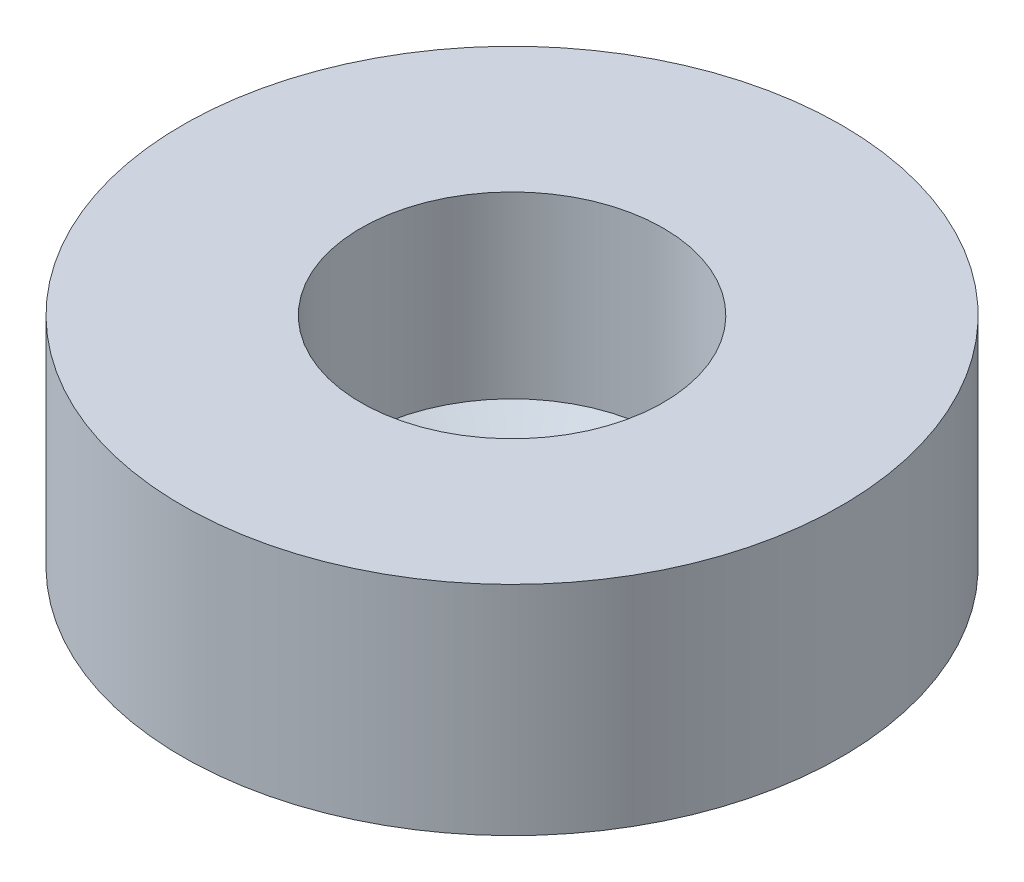
SolidWorks part; units mm, degrees
material "Delrin 2700 NC010, Low Viscosity Acetal Copolymer (SS)"
ref_plane "Front Plane" through (0, 0, 0) normal (0, 0, 1) x (1, 0, 0)
ref_plane "Top Plane" through (0, 0, 0) normal (0, 1, 0) x (1, 0, 0)
ref_plane "Right Plane" through (0, 0, 0) normal (1, 0, 0) x (0, 0, -1)
sketch "Sketch1" plane through (0, 0, 0) normal (0, 0, 1) x (1, 0, 0)
  line L0 (-1.7318, 0) -> (-3, 0.762)
  line L1 (-3, 0.762) -> (-3, 4.318)
  line L2 (-3, 4.318) -> (-6.5405, 4.318)
  line L3 (-6.5405, 4.318) -> (-6.5405, 0)
  line L4 (-6.5405, 0) -> (-1.7318, 0)
  line L5 (0, 0) -> (0, 7.469) construction
  dimension "D1" = 3
  dimension "D2" = 31
  dimension "D3" = 0.762
  dimension "D4" = 4.318
  dimension "D5" = 6.5405
revolve "Revolve1" add sketch "Sketch1" angle 360 about L5
equation "\"D1@Sketch1\"=3mm"
equation "\"D2@Sketch1\"=90-118/2"
equation "\"D5@Sketch1\"=.515/2"
